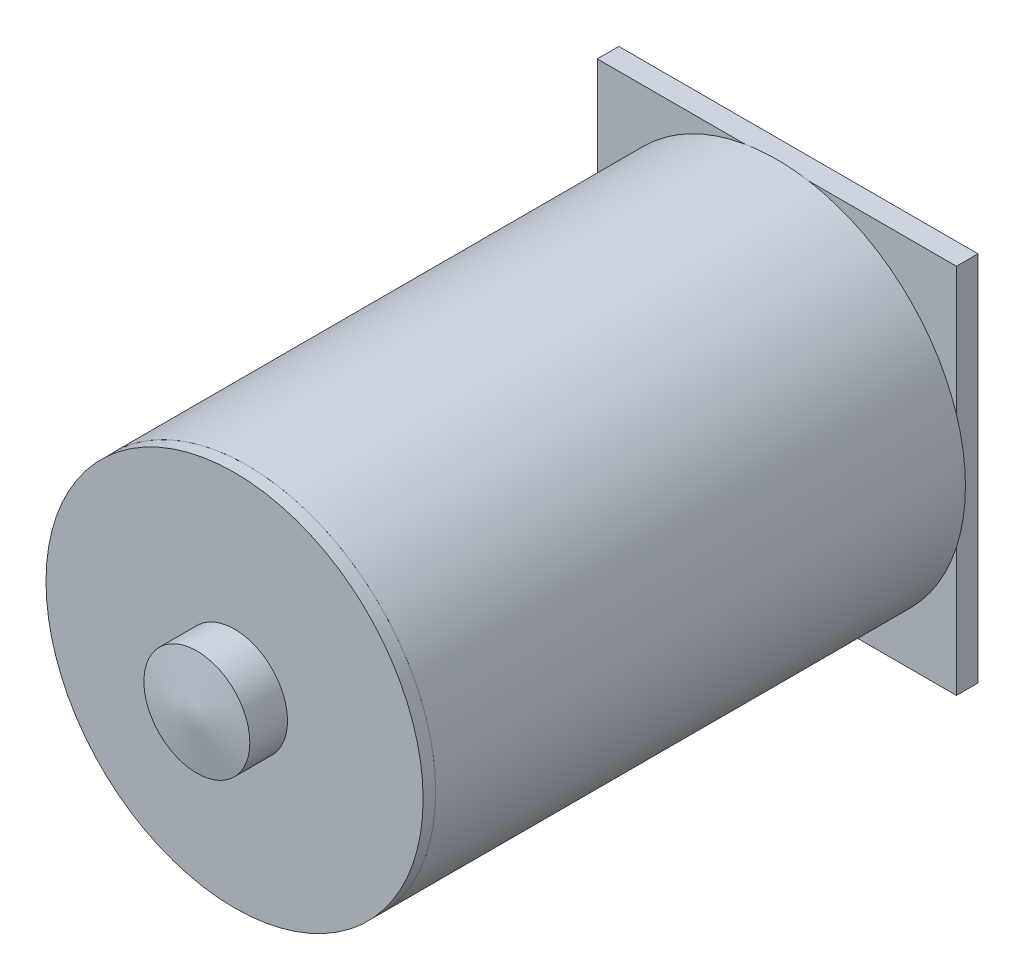
SolidWorks part; units mm, degrees
ref_plane "Front Plane" through (0, 0, 0) normal (0, 0, 1) x (1, 0, 0)
ref_plane "Top Plane" through (0, 0, 0) normal (0, 1, 0) x (1, 0, 0)
ref_plane "Right Plane" through (0, 0, 0) normal (1, 0, 0) x (0, 0, -1)
sketch "Sketch1" plane through (0, 0, 0) normal (0, 0, 1) x (1, 0, 0)
  circle A0 centre (0, 0) radius 10.5
  dimension "D1" = 21
extrude "Boss-Extrude1" add sketch "Sketch1" along normal blind 29.5
sketch "Sketch2" plane through (0, 0, 29.5) normal (0, 0, 1) x (1, 0, 0)
  circle A1 centre (0, 0) radius 10.5
  circle A2 centre (0, 0) radius 10.5
  dimension "D1" = 0
extrude "Boss-Extrude2" add sketch "Sketch2" along normal blind 0.7 separate body
sketch "Sketch3" plane through (0, 0, 0) normal (0, 0, -1) x (-1, 0, 0)
  line L1 (-10, -10.35) -> (10, -10.35)
  line L2 (-10, -10.35) -> (-10, 10.35)
  line L3 (-10, 10.35) -> (10, 10.35)
  line L4 (10, -10.35) -> (10, 10.35)
  line L5 (-10, -10.35) -> (10, 10.35) construction
  line L6 (-10, 10.35) -> (10, -10.35) construction
  point P0 (0, 0)
  dimension "D1" = 20.7
  dimension "D2" = 20
extrude "Boss-Extrude3" add sketch "Sketch3" along normal blind 1.2
sketch "Sketch4" plane through (0, 0, -1.2) normal (0, 0, -1) x (-1, 0, 0)
  circle A0 centre (0, 0) radius 3.85
  dimension "D1" = 7.7
extrude "Cut-Extrude1" cut sketch "Sketch4" against normal blind 25
sketch "Sketch5" plane through (0, 0, 30.2) normal (0, 0, 1) x (1, 0, 0)
  circle A0 centre (0, 0) radius 2.95
  dimension "D1" = 5.9
extrude "Boss-Extrude4" add sketch "Sketch5" along normal blind 2.1
sketch "Sketch6" plane through (0, 0, 32.3) normal (0, 0, 1) x (1, 0, 0)
  circle A1 centre (0, 0) radius 2.95
  circle A2 centre (0, 0) radius 2.95
  dimension "D1" = 0
extrude "Boss-Extrude5" add sketch "Sketch6" along normal blind 10 draft 80
